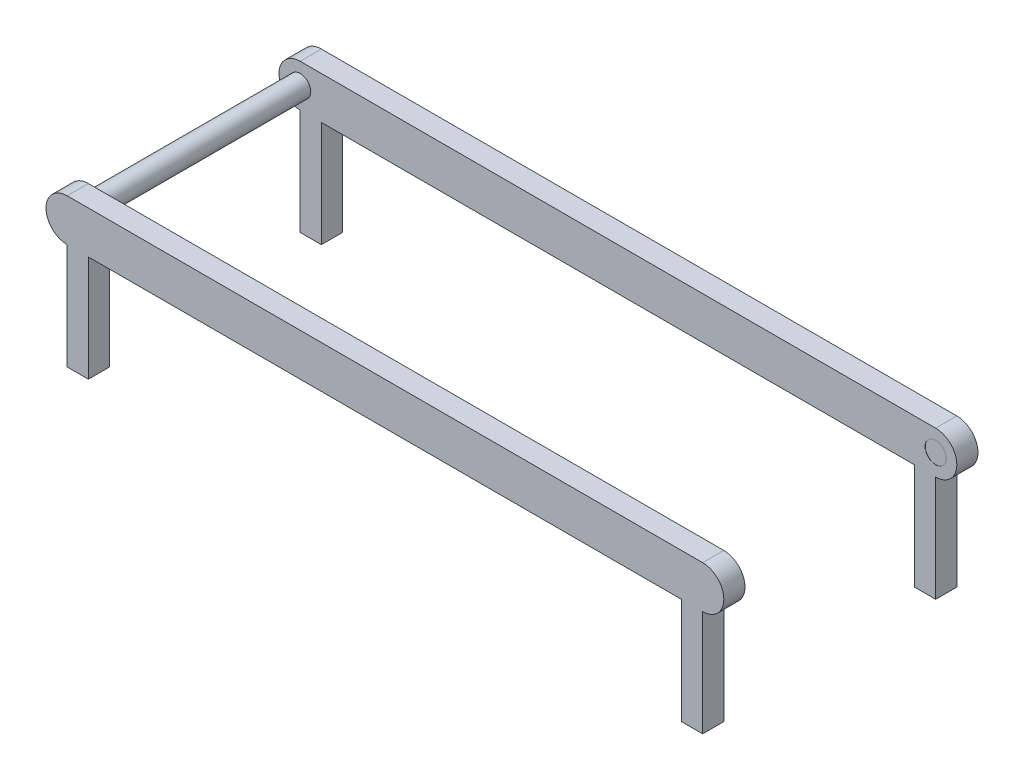
SolidWorks part; units mm, degrees
ref_plane "Alzado" through (0, 0, 0) normal (0, 0, 1) x (1, 0, 0)
ref_plane "Planta" through (0, 0, 0) normal (0, 1, 0) x (1, 0, 0)
ref_plane "Vista lateral" through (0, 0, 0) normal (1, 0, 0) x (0, 0, -1)
sketch "Croquis1" plane through (0, 0, 0) normal (0, 0, 1) x (1, 0, 0)
  line L0 (-150, 0) -> (150, 0) construction
  line L1 (-150, 10) -> (150, 10)
  line L2 (-150, -10) -> (150, -10)
  arc A0 (-150, 10) -> (-150, -10) centre (-150, 0) ccw
  arc A1 (150, -10) -> (150, 10) centre (150, 0) ccw
  point P2 (0, 0)
  dimension "D2" = 10
  dimension "D1" = 300
extrude "Saliente-Extruir1" add sketch "Croquis1" along normal blind 10
sketch "Croquis2" plane through (0, 0, 10) normal (0, 0, 1) x (1, 0, 0)
  circle A0 centre (-150, 0) radius 5
  dimension "D1" = 10
extrude "Saliente-Extruir2" add sketch "Croquis2" along normal blind 100
sketch "Croquis3" plane through (0, 0, 110) normal (0, 0, 1) x (1, 0, 0)
  line L0 (-150, -10) -> (150, -10) construction
  line L1 (-150, -10) -> (150, -10)
  line L2 (-150, 10) -> (150, 10)
  arc A0 (150, -10) -> (150, 10) centre (150, 0) ccw construction
  arc A1 (150, -10) -> (150, 10) centre (150, 0) ccw
  arc A2 (-150, -10) -> (-150, 10) centre (-150, 0) cw
extrude "Saliente-Extruir3" add sketch "Croquis3" along normal blind 10
sketch "Croquis4" plane through (0, -10, 0) normal (0, -1, 0) x (1, 0, 0)
  line L0 (-150, 110) -> (150, 110) construction
  line L1 (-150, 120) -> (-140, 120)
  line L2 (-150, 120) -> (-150, 110)
  line L3 (-150, 110) -> (-140, 110)
  line L4 (-140, 120) -> (-140, 110)
  line L5 (145, 110) -> (155, 110) construction
  line L6 (150, 110) -> (140, 110)
  line L7 (150, 110) -> (150, 120)
  line L8 (150, 120) -> (140, 120)
  line L9 (140, 110) -> (140, 120)
  line L10 (-150, 120) -> (150, 120) construction
  line L11 (-150, 10) -> (150, 10) construction
  line L12 (150, 0) -> (140, 0)
  line L13 (150, 0) -> (150, 10)
  line L14 (150, 10) -> (140, 10)
  line L15 (140, 0) -> (140, 10)
  line L17 (-150, 0) -> (-140, 0)
  line L18 (-150, 0) -> (-150, 10)
  line L19 (-150, 10) -> (-140, 10)
  line L20 (-140, 0) -> (-140, 10)
  dimension "D1" = 10
  dimension "D2" = 10
  dimension "D3" = 10
  dimension "D4" = 10
extrude "Saliente-Extruir4" add sketch "Croquis4" along normal blind 50
sketch "Croquis5" plane through (0, 0, 10) normal (0, 0, 1) x (1, 0, 0)
  circle A0 centre (150, 0) radius 5
  dimension "D1" = 10
extrude "Cortar-Extruir1" cut sketch "Croquis5" against normal blind 0.1
